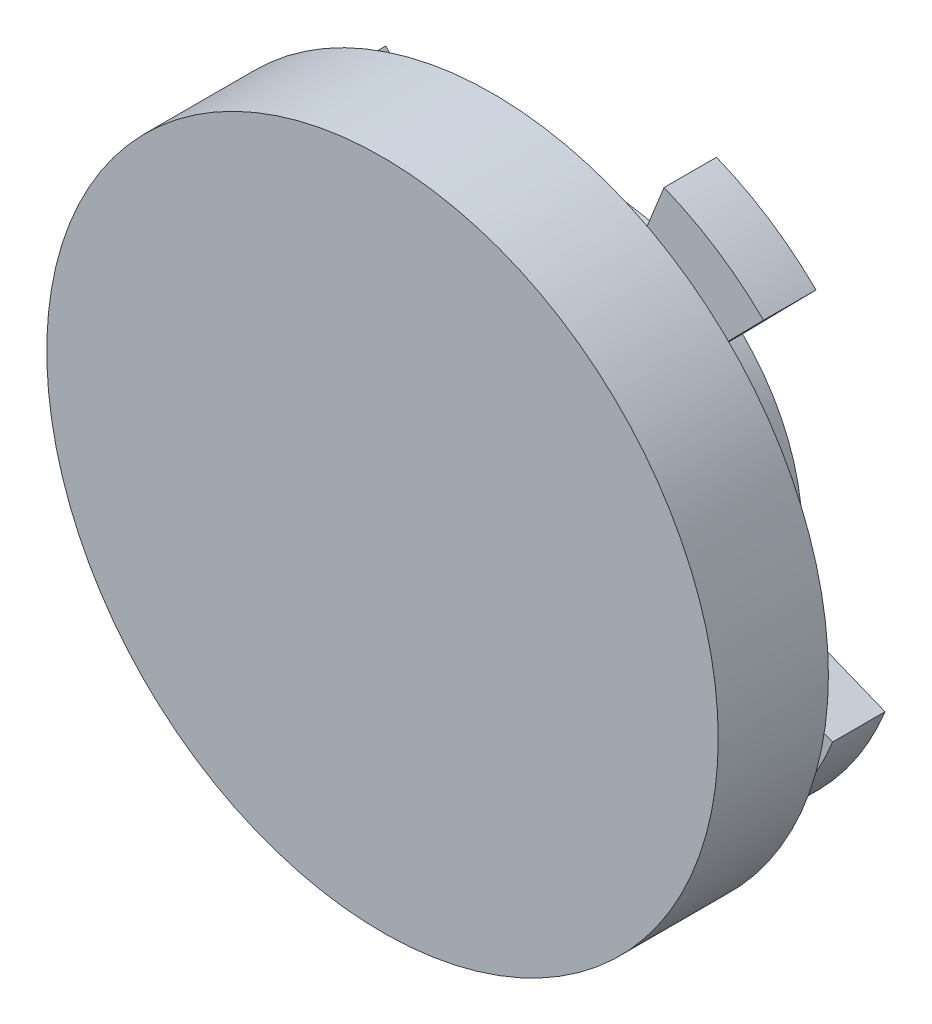
SolidWorks part; units mm, degrees
ref_plane "Front Plane" through (0, 0, 0) normal (0, 0, 1) x (1, 0, 0)
ref_plane "Top Plane" through (0, 0, 0) normal (0, 1, 0) x (1, 0, 0)
ref_plane "Right Plane" through (0, 0, 0) normal (1, 0, 0) x (0, 0, -1)
sketch "Sketch1" plane through (0, 0, 0) normal (0, 0, 1) x (1, 0, 0)
  line L0 (5.4178, 13.4498) -> (3.5496, 8.812)
  line L1 (10.1596, 10.3456) -> (6.6563, 6.7782)
  line L2 (13.4498, -5.4178) -> (8.812, -3.5496)
  line L3 (10.3456, -10.1596) -> (6.7782, -6.6563)
  line L4 (-5.4178, -13.4498) -> (-3.5496, -8.812)
  line L5 (-10.1596, -10.3456) -> (-6.6563, -6.7782)
  line L6 (-13.4498, 5.4178) -> (-8.812, 3.5496)
  line L7 (-10.3456, 10.1596) -> (-6.7782, 6.6563)
  arc A0 (-8.812, 3.5496) -> (-6.6563, -6.7782) centre (0, 0) ccw
  arc A1 (10.1596, 10.3456) -> (5.4178, 13.4498) centre (0, 0) ccw
  arc A2 (10.3456, -10.1596) -> (13.4498, -5.4178) centre (0, 0) ccw
  arc A3 (-10.1596, -10.3456) -> (-5.4178, -13.4498) centre (0, 0) ccw
  arc A4 (-10.3456, 10.1596) -> (-13.4498, 5.4178) centre (0, 0) ccw
  arc A5 (3.5496, 8.812) -> (-6.7782, 6.6563) centre (0, 0) ccw
  arc A6 (8.812, -3.5496) -> (6.6563, 6.7782) centre (0, 0) ccw
  arc A7 (-3.5496, -8.812) -> (6.7782, -6.6563) centre (0, 0) ccw
  point P22 (0, 0)
  dimension "D1" = 29
  dimension "D2" = 19
  dimension "D3" = 4
extrude "Boss-Extrude1" add sketch "Sketch1" along normal blind 2.5
sketch "Sketch2" plane through (0, 0, 2.5) normal (0, 0, 1) x (1, 0, 0)
  arc A1 (8.812, -3.5496) -> (6.6563, 6.7782) centre (0, 0) ccw construction
  circle A3 centre (0, 0) radius 9.5
  dimension "D1" = 0
extrude "Boss-Extrude2" add sketch "Sketch2" along normal blind 3
sketch "Sketch3" plane through (0, 0, 5.5) normal (0, 0, 1) x (1, 0, 0)
  circle A0 centre (0, 0) radius 16
extrude "Boss-Extrude3" add sketch "Sketch3" along normal blind 5 and the other way blind 0.25
